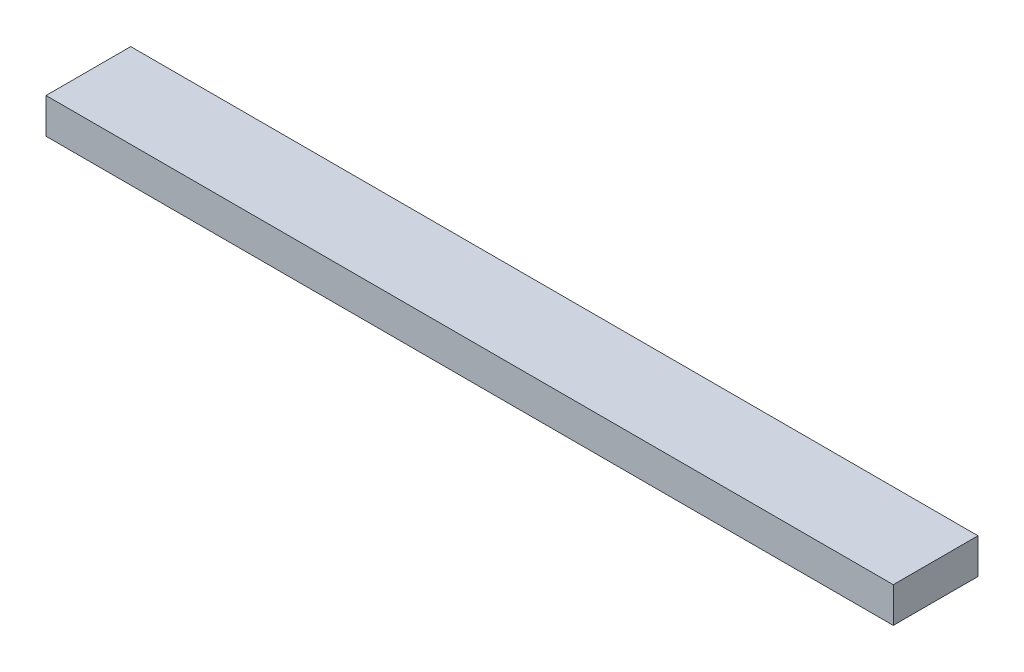
SolidWorks part; units mm, degrees
ref_plane "Front Plane" through (0, 0, 0) normal (0, 0, 1) x (1, 0, 0)
ref_plane "Top Plane" through (0, 0, 0) normal (0, 1, 0) x (1, 0, 0)
ref_plane "Right Plane" through (0, 0, 0) normal (1, 0, 0) x (0, 0, -1)
sketch "Sketch1" plane through (0, 0, 0) normal (0, 1, 0) x (1, 0, 0)
  line L1 (-38.1, -3.81) -> (38.1, -3.81)
  line L2 (-38.1, -3.81) -> (-38.1, 3.81)
  line L3 (-38.1, 3.81) -> (38.1, 3.81)
  line L4 (38.1, -3.81) -> (38.1, 3.81)
  line L5 (-38.1, -3.81) -> (38.1, 3.81) construction
  line L6 (-38.1, 3.81) -> (38.1, -3.81) construction
  point P0 (0, 0)
  dimension "D1" = 7.62
  dimension "D2" = 76.2
extrude "Boss-Extrude1" add sketch "Sketch1" along normal blind 3.175
